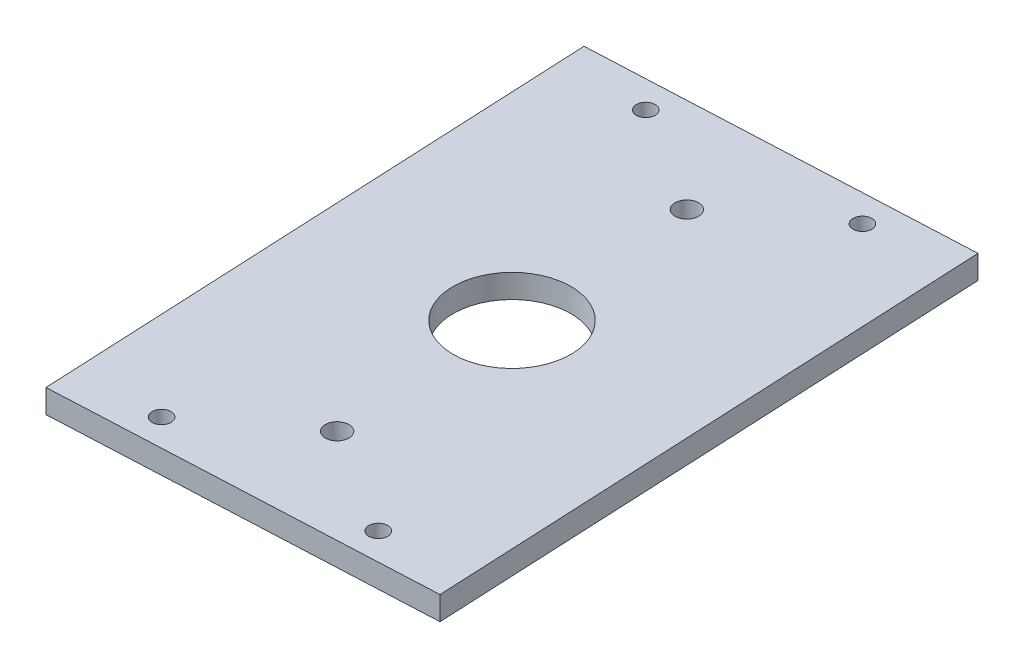
SolidWorks part; units mm, degrees
ref_plane "前视基准面" through (0, 0, 0) normal (0, 0, 1) x (1, 0, 0)
ref_plane "上视基准面" through (0, 0, 0) normal (0, 1, 0) x (1, 0, 0)
ref_plane "右视基准面" through (0, 0, 0) normal (1, 0, 0) x (0, 0, -1)
sketch "草图1" plane through (-72.5871, 0, 457.0277) normal (0, 1, 0) x (0.9989, 0, -0.0469)
  line L4 (133.9362, 393.1216) -> (133.9362, 513.1216)
  line L5 (53.9362, 393.1216) -> (133.9362, 393.1216)
  line L6 (53.9362, 513.1216) -> (53.9362, 393.1216)
  line L7 (133.9362, 513.1216) -> (53.9362, 513.1216)
  line L8 (93.9362, 513.1216) -> (93.9362, 393.1216) construction
  line L9 (133.9362, 453.1216) -> (53.9362, 453.1216) construction
  circle A0 centre (93.9362, 492.1216) radius 2.5
  circle A1 centre (93.9362, 414.1216) radius 2.5
  circle A3 centre (115.9362, 507.1216) radius 2
  circle A4 centre (115.9362, 399.1216) radius 2
  circle A5 centre (71.9362, 507.1216) radius 2
  circle A6 centre (71.9362, 399.1216) radius 2
  circle A7 centre (93.9362, 453.1216) radius 12.5
  point P5 (93.9362, 453.1216)
  dimension "D5" = 4
  dimension "D6" = 25
  dimension "D7" = 5
  dimension "D1" = 120
  dimension "D2" = 80
  dimension "D3" = 6
  dimension "D4" = 18
  dimension "D8" = 78
extrude "凸台-拉伸1" add sketch "草图1" along normal blind 5
